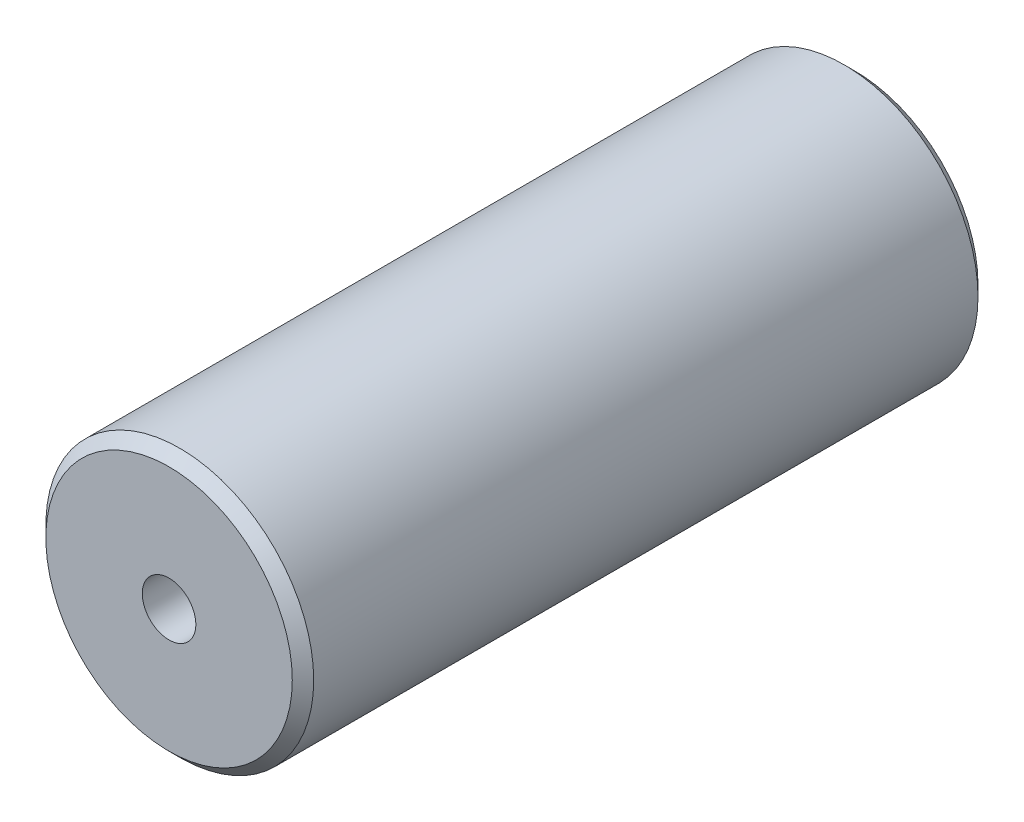
SolidWorks part; units mm, degrees
ref_plane "Front Plane" through (0, 0, 0) normal (0, 0, 1) x (1, 0, 0)
ref_plane "Top Plane" through (0, 0, 0) normal (0, 1, 0) x (1, 0, 0)
ref_plane "Right Plane" through (0, 0, 0) normal (1, 0, 0) x (0, 0, -1)
sketch "Sketch1" plane through (0, 0, 0) normal (0, 0, 1) x (1, 0, 0)
  circle A0 centre (0, 0) radius 12.5
  dimension "D1" = 25
extrude "Boss-Extrude1" add sketch "Sketch1" along normal mid plane 64
chamfer "Chamfer1" distance 1 angle 45 2 edges at (12.5, 0, -32) (12.5, 0, 32)
hole_wizard "Tap Drill for M6 Tap1" positions "Sketch2" profile "Sketch4" hole size "M6" standard "ISO"
sketch "Sketch2" plane through (0, 0, 32) normal (0, 0, 1) x (1, 0, 0)
  point P0 (0, 0)
sketch "Sketch4" plane through (0, 0, 32) normal (1, 0, 0) x (0, -1, 0)
  line L0 (0, 0) -> (0, 14.5022)
  line L1 (0, 14.5022) -> (2.5, 13)
  line L2 (2.5, 13) -> (2.5, 0)
  line L5 (2.5, 0) -> (0, 0)
  line L10 (0, 14.5022) -> (-2.5, 13) construction
  line L11 (0, -6.35) -> (0, 107.95) construction
  dimension "Hole Dia." = 5
  dimension "Hole Depth" = 13
  dimension "Drill Angle" = 118
mirror "Mirror1" about plane through (0, 0, 0) normal (0, 0, 1) of "Tap Drill for M6 Tap1"
